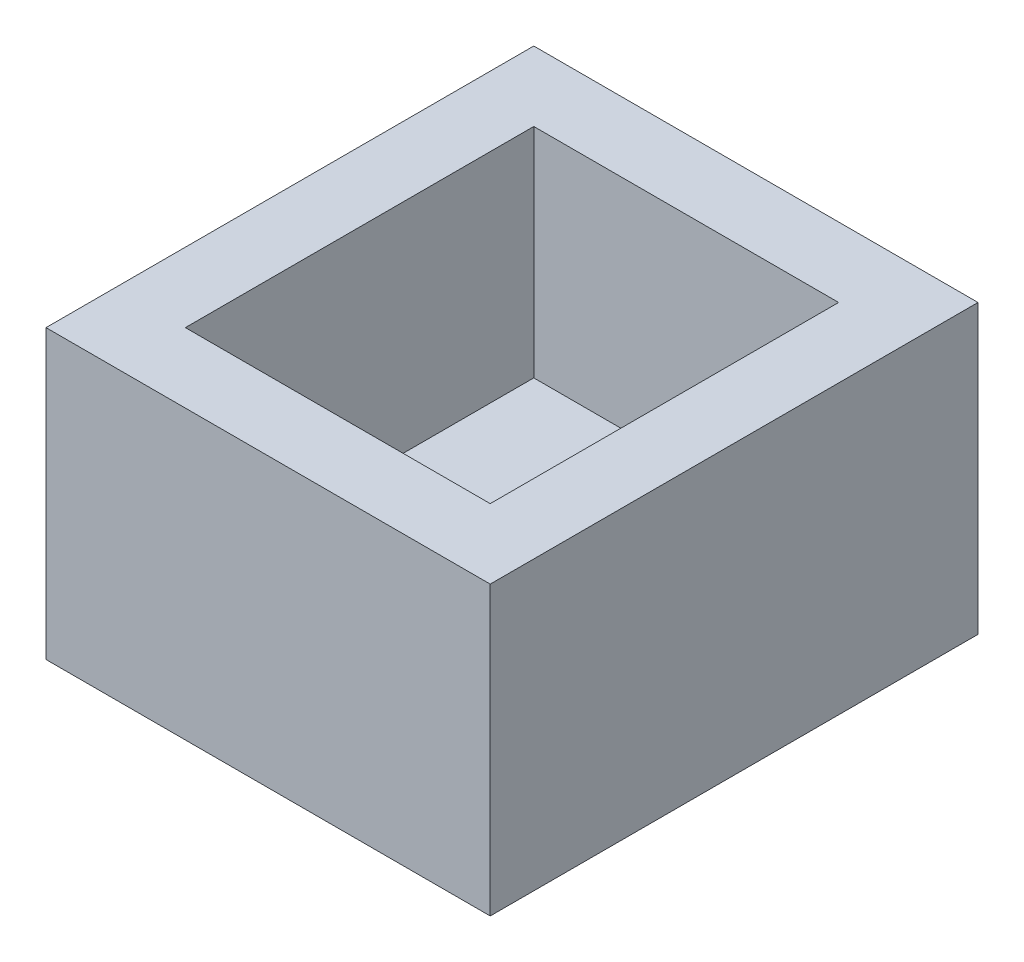
SolidWorks part; units mm, degrees
ref_plane "Front Plane" through (0, 0, 0) normal (0, 0, 1) x (1, 0, 0)
ref_plane "Top Plane" through (0, 0, 0) normal (0, 1, 0) x (1, 0, 0)
ref_plane "Right Plane" through (0, 0, 0) normal (1, 0, 0) x (0, 0, -1)
sketch "Sketch4" plane through (0, 0, 0) normal (0, 1, 0) x (1, 0, 0)
  line L0 (0, 0) -> (0, -112)
  line L5 (0, -112) -> (102, -112)
  line L6 (102, -112) -> (102, 0)
  line L7 (102, 0) -> (0, 0)
  dimension "D1" = 112
  dimension "D2" = 102
extrude "Boss-Extrude4" add sketch "Sketch4" along normal blind 16
sketch "Sketch5" plane through (0, 16, 0) normal (0, 1, 0) x (1, 0, 0)
  line L1 (0, 0) -> (102, 0)
  line L2 (0, 0) -> (0, -112)
  line L3 (0, -112) -> (102, -112)
  line L4 (102, 0) -> (102, -112)
  line L5 (16, -16) -> (86, -16)
  line L6 (16, -16) -> (16, -96)
  line L7 (16, -96) -> (86, -96)
  line L8 (86, -16) -> (86, -96)
  line L10 (0, -112) -> (102, -112) construction
  line L11 (102, -112) -> (102, 0) construction
  dimension "D1" = 16
  dimension "D2" = 16
  dimension "D3" = 16
  dimension "D4" = 16
extrude "Boss-Extrude5" add sketch "Sketch5" along normal blind 50
